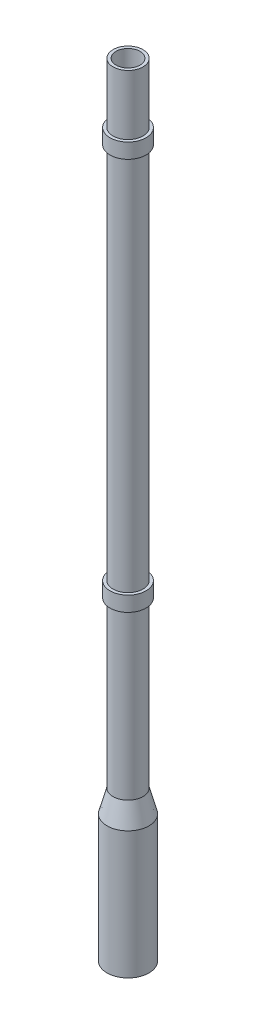
SolidWorks part; units mm, degrees
material "Plain Carbon Steel"
ref_plane "Front Plane" through (0, 0, 0) normal (0, 0, 1) x (1, 0, 0)
ref_plane "Top Plane" through (0, 0, 0) normal (0, 1, 0) x (1, 0, 0)
ref_plane "Right Plane" through (0, 0, 0) normal (1, 0, 0) x (0, 0, -1)
sketch "Sketch1" plane through (0, 0, 0) normal (0, 0, 1) x (1, 0, 0)
  line L0 (0, 0) -> (0, 2110) construction
  line L1 (-70, -74.641) -> (-70, -500)
  line L2 (-50, 0) -> (-50, 2110)
  line L3 (-60, -75.9575) -> (-60, -500)
  line L4 (-40, -1.3165) -> (-60, -75.9575)
  line L5 (-40, -1.3165) -> (-40, 2110)
  line L6 (-50, 0) -> (-70, -74.641)
  line L7 (-70, -500) -> (-60, -500)
  line L8 (-50, 2110) -> (-40, 2110)
  dimension "D1" = 50
  dimension "D2" = 2110
  dimension "D3" = 10
  dimension "D4" = 165
revolve "Revolve1" add sketch "Sketch1" angle 360 about L0
ref_plane "Plane1" through (0, 1860, 0) normal (0, 1, 0) x (1, 0, 0)
sketch "Sketch3" plane through (0, 1860, 0) normal (0, 1, 0) x (1, 0, 0)
  circle A1 centre (0, 0) radius 40
  circle A3 centre (0, 0) radius 60
  dimension "D1" = 20
extrude "Boss-Extrude1" add sketch "Sketch3" along normal blind 50
ref_plane "Plane2" through (0, 600, 0) normal (0, 1, 0) x (1, 0, 0)
sketch "Sketch4" plane through (0, 600, 0) normal (0, 1, 0) x (1, 0, 0)
  circle A0 centre (0, 0) radius 60
  circle A1 centre (0, 0) radius 40
extrude "Boss-Extrude3" add sketch "Sketch4" against normal blind 50
